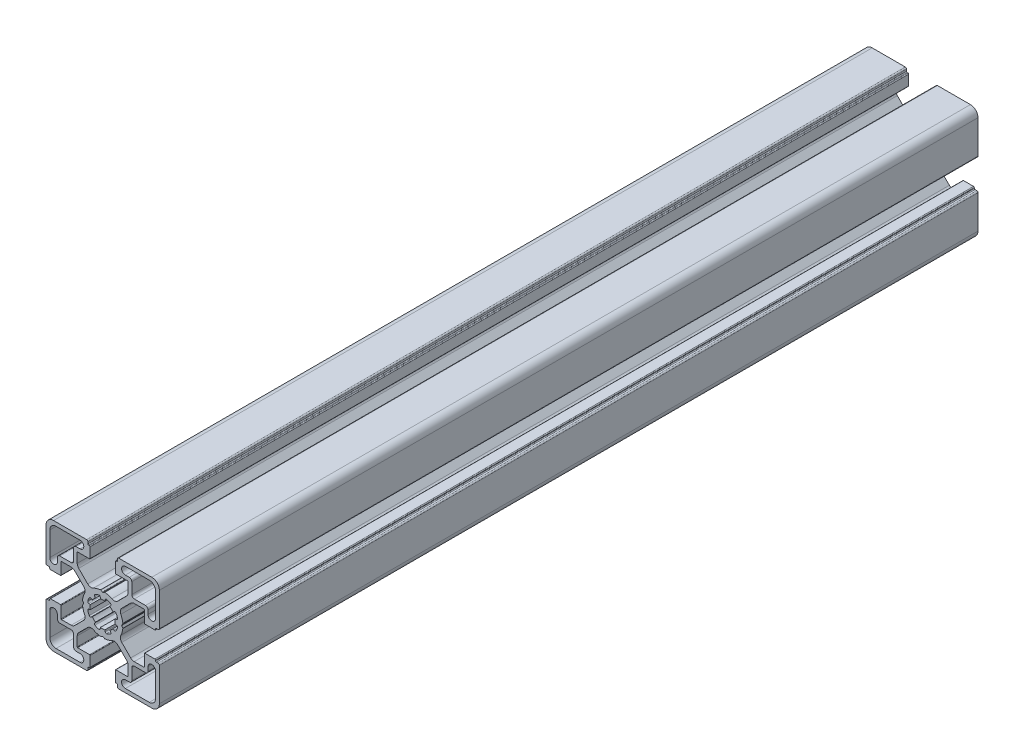
SolidWorks part; units mm, degrees
ref_plane "Plan de face" through (0, 0, 0) normal (0, 0, 1) x (1, 0, 0)
ref_plane "Plan de dessus" through (0, 0, 0) normal (0, 1, 0) x (1, 0, 0)
ref_plane "Plan de droite" through (0, 0, 0) normal (1, 0, 0) x (0, 0, -1)
sketch "Esquisse2" plane through (0, 0, 0) normal (0, 0, 1) x (1, 0, 0)
  line L28 (-195.0842, -352.0697) -> (-194.515, -352.1681)
  line L29 (-195.438, -354.39) -> (-195.9151, -354.0583)
  line L30 (-197.1408, -355.2803) -> (-196.8135, -355.7444)
  line L31 (-199.0372, -356.663) -> (-199.1374, -356.106)
  line L36 (-195.0842, -350.294) -> (-194.515, -350.1956)
  line L37 (-195.438, -347.9737) -> (-195.9151, -348.3053)
  line L38 (-197.1408, -347.0834) -> (-196.8135, -346.6192)
  line L39 (-199.0372, -345.7007) -> (-199.1374, -346.2577)
  line L40 (-200.9723, -356.663) -> (-200.8722, -356.106)
  line L41 (-202.8688, -355.2803) -> (-203.1961, -355.7444)
  line L42 (-204.5715, -354.39) -> (-204.0945, -354.0583)
  line L43 (-204.9253, -352.0697) -> (-205.4945, -352.1681)
  line L44 (-204.9253, -350.294) -> (-205.4945, -350.1956)
  line L45 (-204.5715, -347.9737) -> (-204.0945, -348.3053)
  line L46 (-202.8688, -347.0834) -> (-203.1961, -346.6192)
  line L47 (-200.9723, -345.7007) -> (-200.8722, -346.2577)
  line L105 (-200.0048, -338.2818) -> (-200.0048, -369.1677) construction
  line L107 (-190.0994, -351.1818) -> (-217.4619, -351.1818) construction
  line L108 (-191.0048, -330.1818) -> (-181.5048, -330.1818)
  line L109 (-189.4548, -333.1818) -> (-191.0048, -333.1818)
  line L116 (-221.0047, -332.6818) -> (-221.0047, -342.1816)
  line L117 (-218.0047, -342.1816) -> (-218.0047, -340.6318)
  line L118 (-217.0047, -339.6318) -> (-212.5547, -339.6318)
  line L119 (-211.5547, -338.6318) -> (-211.5547, -334.1818)
  line L120 (-210.5547, -333.1818) -> (-209.0047, -333.1818)
  line L121 (-209.0047, -330.1818) -> (-218.5047, -330.1818)
  line L122 (-188.4548, -338.6318) -> (-188.4548, -334.1818)
  line L123 (-183.0048, -339.6318) -> (-187.4548, -339.6318)
  line L124 (-182.0048, -342.1816) -> (-182.0048, -340.6318)
  line L125 (-179.0048, -332.6818) -> (-179.0048, -342.1816)
  line L126 (-191.0048, -372.1819) -> (-181.5048, -372.1819)
  line L127 (-189.4548, -369.1819) -> (-191.0048, -369.1819)
  line L128 (-188.4548, -363.7319) -> (-188.4548, -368.1819)
  line L129 (-183.0048, -362.7319) -> (-187.4548, -362.7319)
  line L130 (-182.0048, -360.182) -> (-182.0048, -361.7319)
  line L131 (-179.0048, -369.6819) -> (-179.0048, -360.182)
  line L196 (-192.4647, -351.135) -> (-192.0308, -350.3893)
  line L197 (-192.4413, -345.3231) -> (-188.875, -341.7569)
  line L198 (-187.5, -341.1873) -> (-183.6879, -341.1873)
  line L199 (-183.4879, -341.3873) -> (-183.4879, -345.9818)
  line L200 (-183.2879, -346.1818) -> (-179.2852, -346.1818)
  line L201 (-178.9852, -345.8818) -> (-178.9852, -345.6818)
  line L202 (-178.6852, -345.3818) -> (-178.0048, -345.3818)
  line L203 (-177.5048, -344.8818) -> (-177.5048, -331.6818)
  line L204 (-180.5048, -328.6818) -> (-193.6291, -328.6818)
  line L205 (-194.1291, -329.1818) -> (-194.1291, -329.8818)
  line L206 (-194.4291, -330.1818) -> (-194.7048, -330.1818)
  line L207 (-195.0048, -330.4818) -> (-195.0048, -334.515)
  line L208 (-194.8048, -334.715) -> (-190.0994, -334.715)
  line L209 (-189.8994, -334.915) -> (-189.8994, -338.7103)
  line L210 (-190.4852, -340.1245) -> (-194.0599, -343.6992)
  line L211 (-199.25, -343.207) -> (-199.8921, -343.5749)
  line L212 (-200.1174, -343.5749) -> (-200.7595, -343.207)
  line L213 (-205.9497, -343.6992) -> (-209.5244, -340.1245)
  line L214 (-210.1102, -338.7103) -> (-210.1102, -334.915)
  line L215 (-209.9102, -334.715) -> (-205.2048, -334.715)
  line L216 (-205.0048, -334.515) -> (-205.0048, -330.4818)
  line L217 (-205.3048, -330.1818) -> (-205.5805, -330.1818)
  line L218 (-205.8805, -329.8818) -> (-205.8805, -329.1818)
  line L219 (-206.3805, -328.6818) -> (-219.5047, -328.6818)
  line L220 (-222.5047, -331.6818) -> (-222.5047, -344.8818)
  line L221 (-222.0047, -345.3818) -> (-221.3244, -345.3818)
  line L222 (-221.0244, -345.6818) -> (-221.0244, -345.8818)
  line L223 (-220.7244, -346.1818) -> (-216.7217, -346.1818)
  line L224 (-216.5217, -345.9818) -> (-216.5217, -341.3873)
  line L225 (-216.3217, -341.1873) -> (-212.5095, -341.1873)
  line L226 (-211.1345, -341.7569) -> (-207.5682, -345.3231)
  line L227 (-207.9787, -350.3893) -> (-207.5448, -351.135)
  line L228 (-207.5448, -351.2287) -> (-207.9787, -351.9744)
  line L229 (-207.5682, -357.0405) -> (-211.1345, -360.6068)
  line L230 (-212.5095, -361.1764) -> (-216.3217, -361.1764)
  line L231 (-216.5217, -360.9764) -> (-216.5217, -356.3819)
  line L232 (-216.7217, -356.1819) -> (-220.7244, -356.1819)
  line L233 (-221.0244, -356.4819) -> (-221.0244, -356.6818)
  line L234 (-221.3244, -356.9818) -> (-222.0047, -356.9818)
  line L235 (-222.5047, -357.4818) -> (-222.5047, -370.6819)
  line L236 (-219.5047, -373.6819) -> (-206.3805, -373.6819)
  line L237 (-205.8805, -373.1819) -> (-205.8805, -372.4819)
  line L238 (-205.5805, -372.1819) -> (-205.3048, -372.1819)
  line L239 (-205.0048, -371.8819) -> (-205.0048, -367.8487)
  line L240 (-205.2048, -367.6487) -> (-209.9102, -367.6487)
  line L241 (-210.1102, -367.4487) -> (-210.1102, -363.6534)
  line L242 (-209.5244, -362.2392) -> (-205.9497, -358.6645)
  line L243 (-200.7595, -359.1566) -> (-200.1174, -358.7888)
  line L244 (-199.8921, -358.7888) -> (-199.25, -359.1566)
  line L245 (-194.0599, -358.6645) -> (-190.4852, -362.2392)
  line L246 (-189.8994, -363.6534) -> (-189.8994, -367.4487)
  line L247 (-190.0994, -367.6487) -> (-194.8048, -367.6487)
  line L248 (-195.0048, -367.8487) -> (-195.0048, -371.8819)
  line L249 (-194.7048, -372.1819) -> (-194.4291, -372.1819)
  line L250 (-194.1291, -372.4819) -> (-194.1291, -373.1819)
  line L251 (-193.6291, -373.6819) -> (-180.5048, -373.6819)
  line L252 (-177.5048, -370.6819) -> (-177.5048, -357.4818)
  line L253 (-178.0048, -356.9818) -> (-178.6852, -356.9818)
  line L254 (-178.9852, -356.6818) -> (-178.9852, -356.4819)
  line L255 (-179.2852, -356.1819) -> (-183.2879, -356.1819)
  line L256 (-183.4879, -356.3819) -> (-183.4879, -360.9764)
  line L257 (-183.6879, -361.1764) -> (-187.5, -361.1764)
  line L258 (-188.875, -360.6068) -> (-192.4413, -357.0405)
  line L259 (-192.0308, -351.9744) -> (-192.4647, -351.2287)
  line L260 (-209.0047, -372.1819) -> (-218.5047, -372.1819)
  line L261 (-210.5547, -369.1819) -> (-209.0047, -369.1819)
  line L262 (-211.5547, -363.7319) -> (-211.5547, -368.1819)
  line L263 (-217.0047, -362.7319) -> (-212.5547, -362.7319)
  line L264 (-218.0047, -360.182) -> (-218.0047, -361.7319)
  line L265 (-221.0047, -369.6819) -> (-221.0047, -360.182)
  arc A63 (-194.515, -352.1681) -> (-194.0979, -352.793) centre (-194.5809, -352.6637) cw
  arc A64 (-194.0979, -352.793) -> (-194.7023, -354.2383) centre (-199.9813, -351.1818) cw
  arc A65 (-194.7023, -354.2383) -> (-195.438, -354.39) centre (-195.1368, -353.9909) cw
  arc A66 (-195.9151, -354.0583) -> (-197.1408, -355.2803) centre (-200.0048, -351.1818) cw
  arc A67 (-196.8135, -355.7444) -> (-196.9604, -356.4813) centre (-197.2105, -356.0483) cw
  arc A68 (-196.9604, -356.4813) -> (-198.4097, -357.0759) centre (-199.9813, -351.1818) cw
  arc A69 (-198.4097, -357.0759) -> (-199.0372, -356.663) centre (-198.5421, -356.5938) cw
  arc A70 (-199.1374, -356.106) -> (-200.8722, -356.106) centre (-200.0048, -351.1818) cw
  arc A71 (-201.5998, -357.0759) -> (-200.9723, -356.663) centre (-201.4675, -356.5938) ccw
  arc A81 (-195.0842, -352.0697) -> (-195.0842, -350.294) centre (-200.0048, -351.1818) ccw
  arc A82 (-194.515, -350.1956) -> (-194.0979, -349.5706) centre (-194.5809, -349.7) ccw
  arc A83 (-194.0979, -349.5706) -> (-194.7023, -348.1254) centre (-199.9813, -351.1818) ccw
  arc A84 (-194.7023, -348.1254) -> (-195.438, -347.9737) centre (-195.1368, -348.3728) ccw
  arc A85 (-195.9151, -348.3053) -> (-197.1408, -347.0834) centre (-200.0048, -351.1818) ccw
  arc A86 (-196.8135, -346.6192) -> (-196.9604, -345.8824) centre (-197.2105, -346.3153) ccw
  arc A87 (-196.9604, -345.8824) -> (-198.4097, -345.2878) centre (-199.9813, -351.1818) ccw
  arc A88 (-198.4097, -345.2878) -> (-199.0372, -345.7007) centre (-198.5421, -345.7699) ccw
  arc A89 (-199.1374, -346.2577) -> (-200.8722, -346.2577) centre (-200.0048, -351.1818) ccw
  arc A90 (-203.0492, -356.4813) -> (-201.5998, -357.0759) centre (-200.0282, -351.1818) ccw
  arc A91 (-203.1961, -355.7444) -> (-203.0492, -356.4813) centre (-202.799, -356.0483) ccw
  arc A92 (-204.0945, -354.0583) -> (-202.8688, -355.2803) centre (-200.0048, -351.1818) ccw
  arc A93 (-205.3073, -354.2383) -> (-204.5715, -354.39) centre (-204.8728, -353.9909) ccw
  arc A94 (-205.9116, -352.793) -> (-205.3073, -354.2383) centre (-200.0282, -351.1818) ccw
  arc A95 (-205.4945, -352.1681) -> (-205.9116, -352.793) centre (-205.4286, -352.6637) ccw
  arc A96 (-204.9253, -352.0697) -> (-204.9253, -350.294) centre (-200.0048, -351.1818) cw
  arc A97 (-205.4945, -350.1956) -> (-205.9116, -349.5706) centre (-205.4286, -349.7) cw
  arc A98 (-205.9116, -349.5706) -> (-205.3073, -348.1254) centre (-200.0282, -351.1818) cw
  arc A99 (-205.3073, -348.1254) -> (-204.5715, -347.9737) centre (-204.8728, -348.3728) cw
  arc A100 (-204.0945, -348.3053) -> (-202.8688, -347.0834) centre (-200.0048, -351.1818) cw
  arc A101 (-203.1961, -346.6192) -> (-203.0492, -345.8824) centre (-202.799, -346.3153) cw
  arc A102 (-203.0492, -345.8824) -> (-201.5998, -345.2878) centre (-200.0282, -351.1818) cw
  arc A103 (-201.5998, -345.2878) -> (-200.9723, -345.7007) centre (-201.4675, -345.7699) cw
  arc A128 (-181.5048, -330.1818) -> (-179.0048, -332.6818) centre (-181.5048, -332.6818) cw
  arc A129 (-191.0048, -333.1818) -> (-191.0048, -330.1818) centre (-191.0048, -331.6818) cw
  arc A130 (-189.4548, -333.1818) -> (-188.4548, -334.1818) centre (-189.4548, -334.1818) cw
  arc A131 (-187.4548, -339.6318) -> (-188.4548, -338.6318) centre (-187.4548, -338.6318) cw
  arc A132 (-183.0048, -339.6318) -> (-182.0048, -340.6318) centre (-183.0048, -340.6318) cw
  arc A133 (-179.0048, -342.1816) -> (-182.0048, -342.1816) centre (-180.5048, -342.1816) cw
  arc A140 (-221.0047, -342.1816) -> (-218.0047, -342.1816) centre (-219.5047, -342.1816) ccw
  arc A141 (-217.0047, -339.6318) -> (-218.0047, -340.6318) centre (-217.0047, -340.6318) ccw
  arc A142 (-212.5547, -339.6318) -> (-211.5547, -338.6318) centre (-212.5547, -338.6318) ccw
  arc A143 (-210.5547, -333.1818) -> (-211.5547, -334.1818) centre (-210.5547, -334.1818) ccw
  arc A144 (-209.0047, -333.1818) -> (-209.0047, -330.1818) centre (-209.0047, -331.6818) ccw
  arc A145 (-218.5047, -330.1818) -> (-221.0047, -332.6818) centre (-218.5047, -332.6818) ccw
  arc A146 (-191.0048, -369.1819) -> (-191.0048, -372.1819) centre (-191.0048, -370.6819) ccw
  arc A147 (-189.4548, -369.1819) -> (-188.4548, -368.1819) centre (-189.4548, -368.1819) ccw
  arc A148 (-187.4548, -362.7319) -> (-188.4548, -363.7319) centre (-187.4548, -363.7319) ccw
  arc A149 (-183.0048, -362.7319) -> (-182.0048, -361.7319) centre (-183.0048, -361.7319) ccw
  arc A150 (-179.0048, -360.182) -> (-182.0048, -360.182) centre (-180.5048, -360.182) ccw
  arc A151 (-181.5048, -372.1819) -> (-179.0048, -369.6819) centre (-181.5048, -369.6819) ccw
  arc A152 (-218.5047, -372.1819) -> (-221.0047, -369.6819) centre (-218.5047, -369.6819) cw
  arc A153 (-209.0047, -369.1819) -> (-209.0047, -372.1819) centre (-209.0047, -370.6819) cw
  arc A154 (-210.5547, -369.1819) -> (-211.5547, -368.1819) centre (-210.5547, -368.1819) cw
  arc A155 (-212.5547, -362.7319) -> (-211.5547, -363.7319) centre (-212.5547, -363.7319) cw
  arc A156 (-217.0047, -362.7319) -> (-218.0047, -361.7319) centre (-217.0047, -361.7319) cw
  arc A157 (-221.0047, -360.182) -> (-218.0047, -360.182) centre (-219.5047, -360.182) cw
  arc A254 (-192.4647, -351.135) -> (-192.4734, -351.1818) centre (-192.2739, -351.1948) ccw
  arc A255 (-192.0308, -350.3893) -> (-192.0048, -350.2678) centre (-192.2037, -350.2887) ccw
  arc A256 (-192.0048, -350.2678) -> (-192.8044, -347.57) centre (-199.9552, -351.157) ccw
  arc A257 (-192.4413, -345.3231) -> (-192.8044, -347.57) centre (-191.0663, -346.6981) ccw
  arc A258 (-187.5, -341.1873) -> (-188.875, -341.7569) centre (-187.5, -343.1318) ccw
  arc A259 (-183.4879, -341.3873) -> (-183.6879, -341.1873) centre (-183.6879, -341.3873) ccw
  arc A260 (-183.4879, -345.9818) -> (-183.2879, -346.1818) centre (-183.2879, -345.9818) ccw
  arc A261 (-179.2852, -346.1818) -> (-178.9852, -345.8818) centre (-179.2852, -345.8818) ccw
  arc A262 (-178.6852, -345.3818) -> (-178.9852, -345.6818) centre (-178.6852, -345.6818) ccw
  arc A263 (-178.0048, -345.3818) -> (-177.5048, -344.8818) centre (-178.0048, -344.8818) ccw
  arc A264 (-177.5048, -331.6818) -> (-180.5048, -328.6818) centre (-180.5048, -331.6818) ccw
  arc A265 (-193.6291, -328.6818) -> (-194.1291, -329.1818) centre (-193.6291, -329.1818) ccw
  arc A266 (-194.4291, -330.1818) -> (-194.1291, -329.8818) centre (-194.4291, -329.8818) ccw
  arc A267 (-194.7048, -330.1818) -> (-195.0048, -330.4818) centre (-194.7048, -330.4818) ccw
  arc A268 (-195.0048, -334.515) -> (-194.8048, -334.715) centre (-194.8048, -334.515) ccw
  arc A269 (-189.8994, -334.915) -> (-190.0994, -334.715) centre (-190.0994, -334.915) ccw
  arc A270 (-190.4852, -340.1245) -> (-189.8994, -338.7103) centre (-191.8994, -338.7103) ccw
  arc A271 (-196.3383, -344.0086) -> (-194.0599, -343.6992) centre (-195.4193, -342.2322) ccw
  arc A272 (-196.3383, -344.0086) -> (-199.1284, -343.1818) centre (-199.9813, -351.1818) ccw
  arc A273 (-199.1284, -343.1818) -> (-199.25, -343.207) centre (-199.1506, -343.3806) ccw
  arc A274 (-200.0048, -343.6509) -> (-199.8921, -343.5749) centre (-200.0537, -343.457) ccw
  arc A275 (-200.1174, -343.5749) -> (-200.0048, -343.6509) centre (-199.9559, -343.457) ccw
  arc A276 (-200.7595, -343.207) -> (-200.8812, -343.1818) centre (-200.8589, -343.3806) ccw
  arc A277 (-200.8812, -343.1818) -> (-203.6713, -344.0086) centre (-200.0282, -351.1818) ccw
  arc A278 (-205.9497, -343.6992) -> (-203.6713, -344.0086) centre (-204.5903, -342.2322) ccw
  arc A279 (-210.1102, -338.7103) -> (-209.5244, -340.1245) centre (-208.1102, -338.7103) ccw
  arc A280 (-209.9102, -334.715) -> (-210.1102, -334.915) centre (-209.9102, -334.915) ccw
  arc A281 (-205.2048, -334.715) -> (-205.0048, -334.515) centre (-205.2048, -334.515) ccw
  arc A282 (-205.0048, -330.4818) -> (-205.3048, -330.1818) centre (-205.3048, -330.4818) ccw
  arc A283 (-205.8805, -329.8818) -> (-205.5805, -330.1818) centre (-205.5805, -329.8818) ccw
  arc A284 (-205.8805, -329.1818) -> (-206.3805, -328.6818) centre (-206.3805, -329.1818) ccw
  arc A285 (-219.5047, -328.6818) -> (-222.5047, -331.6818) centre (-219.5047, -331.6818) ccw
  arc A286 (-222.5047, -344.8818) -> (-222.0047, -345.3818) centre (-222.0047, -344.8818) ccw
  arc A287 (-221.0244, -345.6818) -> (-221.3244, -345.3818) centre (-221.3244, -345.6818) ccw
  arc A288 (-221.0244, -345.8818) -> (-220.7244, -346.1818) centre (-220.7244, -345.8818) ccw
  arc A289 (-216.7217, -346.1818) -> (-216.5217, -345.9818) centre (-216.7217, -345.9818) ccw
  arc A290 (-216.3217, -341.1873) -> (-216.5217, -341.3873) centre (-216.3217, -341.3873) ccw
  arc A291 (-211.1345, -341.7569) -> (-212.5095, -341.1873) centre (-212.5095, -343.1318) ccw
  arc A292 (-207.2051, -347.57) -> (-207.5682, -345.3231) centre (-208.9432, -346.6981) ccw
  arc A293 (-207.2051, -347.57) -> (-208.0048, -350.2678) centre (-200.0543, -351.157) ccw
  arc A294 (-208.0048, -350.2678) -> (-207.9787, -350.3893) centre (-207.8059, -350.2887) ccw
  arc A295 (-207.5361, -351.1818) -> (-207.5448, -351.135) centre (-207.7357, -351.1948) ccw
  arc A296 (-207.5448, -351.2287) -> (-207.5361, -351.1818) centre (-207.7357, -351.1689) ccw
  arc A297 (-207.9787, -351.9744) -> (-208.0048, -352.0959) centre (-207.8059, -352.075) ccw
  arc A298 (-208.0048, -352.0959) -> (-207.2051, -354.7937) centre (-200.0543, -351.2067) ccw
  arc A299 (-207.5682, -357.0405) -> (-207.2051, -354.7937) centre (-208.9432, -355.6656) ccw
  arc A300 (-212.5095, -361.1764) -> (-211.1345, -360.6068) centre (-212.5095, -359.2319) ccw
  arc A301 (-216.5217, -360.9764) -> (-216.3217, -361.1764) centre (-216.3217, -360.9764) ccw
  arc A302 (-216.5217, -356.3819) -> (-216.7217, -356.1819) centre (-216.7217, -356.3819) ccw
  arc A303 (-220.7244, -356.1819) -> (-221.0244, -356.4819) centre (-220.7244, -356.4819) ccw
  arc A304 (-221.3244, -356.9818) -> (-221.0244, -356.6818) centre (-221.3244, -356.6818) ccw
  arc A305 (-222.0047, -356.9818) -> (-222.5047, -357.4818) centre (-222.0047, -357.4818) ccw
  arc A306 (-222.5047, -370.6819) -> (-219.5047, -373.6819) centre (-219.5047, -370.6819) ccw
  arc A307 (-206.3805, -373.6819) -> (-205.8805, -373.1819) centre (-206.3805, -373.1819) ccw
  arc A308 (-205.5805, -372.1819) -> (-205.8805, -372.4819) centre (-205.5805, -372.4819) ccw
  arc A309 (-205.3048, -372.1819) -> (-205.0048, -371.8819) centre (-205.3048, -371.8819) ccw
  arc A310 (-205.0048, -367.8487) -> (-205.2048, -367.6487) centre (-205.2048, -367.8487) ccw
  arc A311 (-210.1102, -367.4487) -> (-209.9102, -367.6487) centre (-209.9102, -367.4487) ccw
  arc A312 (-209.5244, -362.2392) -> (-210.1102, -363.6534) centre (-208.1102, -363.6534) ccw
  arc A313 (-203.6713, -358.3551) -> (-205.9497, -358.6645) centre (-204.5903, -360.1315) ccw
  arc A314 (-203.6713, -358.3551) -> (-200.8812, -359.1819) centre (-200.0282, -351.1818) ccw
  arc A315 (-200.8812, -359.1819) -> (-200.7595, -359.1566) centre (-200.8589, -358.9831) ccw
  arc A316 (-200.0048, -358.7128) -> (-200.1174, -358.7888) centre (-199.9559, -358.9067) ccw
  arc A317 (-199.8921, -358.7888) -> (-200.0048, -358.7128) centre (-200.0537, -358.9067) ccw
  arc A318 (-199.25, -359.1566) -> (-199.1284, -359.1819) centre (-199.1506, -358.9831) ccw
  arc A319 (-199.1284, -359.1819) -> (-196.3383, -358.3551) centre (-199.9813, -351.1818) ccw
  arc A320 (-194.0599, -358.6645) -> (-196.3383, -358.3551) centre (-195.4193, -360.1315) ccw
  arc A321 (-189.8994, -363.6534) -> (-190.4852, -362.2392) centre (-191.8994, -363.6534) ccw
  arc A322 (-190.0994, -367.6487) -> (-189.8994, -367.4487) centre (-190.0994, -367.4487) ccw
  arc A323 (-194.8048, -367.6487) -> (-195.0048, -367.8487) centre (-194.8048, -367.8487) ccw
  arc A324 (-195.0048, -371.8819) -> (-194.7048, -372.1819) centre (-194.7048, -371.8819) ccw
  arc A325 (-194.1291, -372.4819) -> (-194.4291, -372.1819) centre (-194.4291, -372.4819) ccw
  arc A326 (-194.1291, -373.1819) -> (-193.6291, -373.6819) centre (-193.6291, -373.1819) ccw
  arc A327 (-180.5048, -373.6819) -> (-177.5048, -370.6819) centre (-180.5048, -370.6819) ccw
  arc A328 (-177.5048, -357.4818) -> (-178.0048, -356.9818) centre (-178.0048, -357.4818) ccw
  arc A329 (-178.9852, -356.6818) -> (-178.6852, -356.9818) centre (-178.6852, -356.6818) ccw
  arc A330 (-178.9852, -356.4819) -> (-179.2852, -356.1819) centre (-179.2852, -356.4819) ccw
  arc A331 (-183.2879, -356.1819) -> (-183.4879, -356.3819) centre (-183.2879, -356.3819) ccw
  arc A332 (-183.6879, -361.1764) -> (-183.4879, -360.9764) centre (-183.6879, -360.9764) ccw
  arc A333 (-188.875, -360.6068) -> (-187.5, -361.1764) centre (-187.5, -359.2319) ccw
  arc A334 (-192.8044, -354.7937) -> (-192.4413, -357.0405) centre (-191.0663, -355.6656) ccw
  arc A335 (-192.8044, -354.7937) -> (-192.0048, -352.0959) centre (-199.9552, -351.2067) ccw
  arc A336 (-192.0048, -352.0959) -> (-192.0308, -351.9744) centre (-192.2037, -352.075) ccw
  arc A337 (-192.4734, -351.1818) -> (-192.4647, -351.2287) centre (-192.2739, -351.1689) ccw
extrude "Boss.-Extru.1" add sketch "Esquisse2" along normal blind 325
